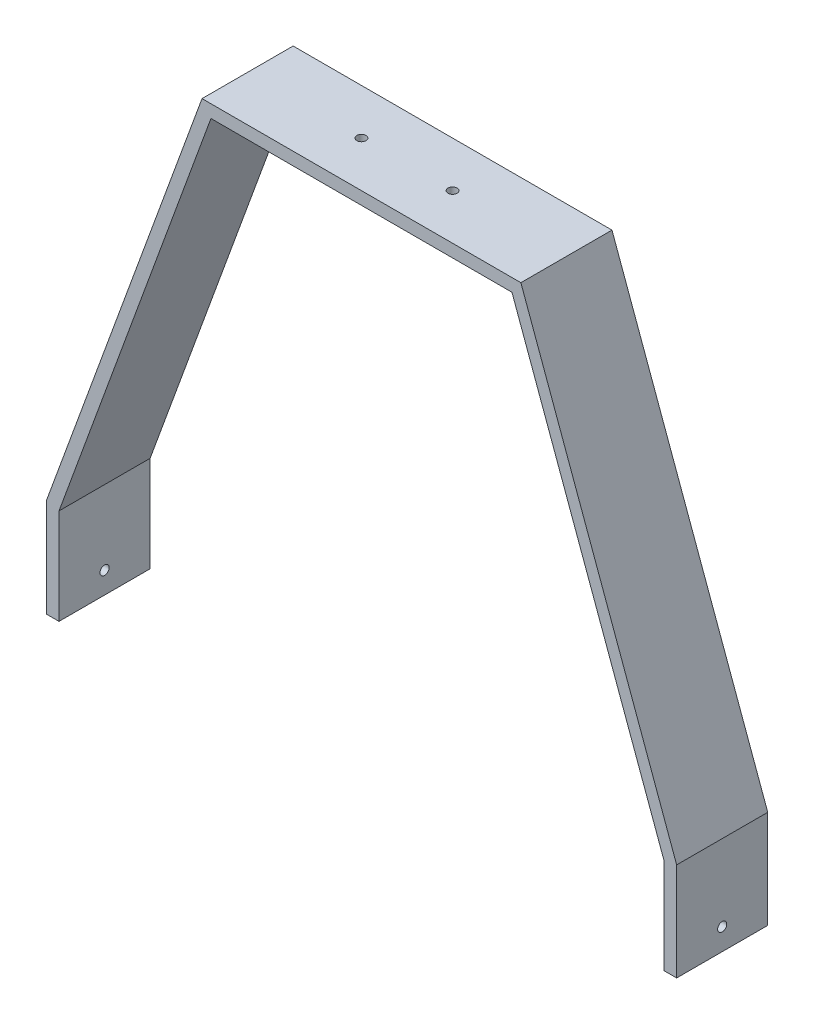
SolidWorks part; units mm, degrees
ref_plane "Front Plane" through (0, 0, 0) normal (0, 0, 1) x (1, 0, 0)
ref_plane "Top Plane" through (0, 0, 0) normal (0, 1, 0) x (1, 0, 0)
ref_plane "Right Plane" through (0, 0, 0) normal (1, 0, 0) x (0, 0, -1)
sketch "Sketch1" plane through (0, 0, 0) normal (0, 0, 1) x (1, 0, 0)
  line L0 (0, 0) -> (175, 0) construction
  line L1 (0, 0) -> (-85.5, -234)
  line L2 (87.5, 0) -> (87.5, 70.6967) construction
  line L4 (4.8949, -7) -> (-78.5, -235.2388)
  line L5 (175, -59.8989) -> (0, -59.8989) construction
  line L6 (175, -59.8989) -> (175, 90.1011) construction
  line L7 (175, 90.1011) -> (0, 90.1011) construction
  line L8 (0, -59.8989) -> (0, 90.1011) construction
  line L11 (170.1051, -7) -> (253.5, -235.2388)
  line L12 (175, 0) -> (260.5, -234)
  line L15 (0, 0) -> (175, 0)
  line L16 (170.1051, -7) -> (4.8949, -7)
  line L17 (87.5, 0) -> (87.5, -45.9968) construction
  line L19 (260.5, -234) -> (260.5, -287.7575)
  line L20 (260.5, -287.7575) -> (253.5, -287.7575)
  line L21 (253.5, -235.2388) -> (253.5, -287.7575)
  line L22 (-85.5, -287.7575) -> (-78.5, -287.7575)
  line L23 (-78.5, -235.2388) -> (-78.5, -287.7575)
  line L25 (-85.5, -234) -> (-85.5, -287.7575)
  point P17 (251.6016, -230.0431)
  dimension "D1" = 175
  dimension "D2" = 234
  dimension "D3" = 85.5
  dimension "D4" = 150
  dimension "D5" = 7
  dimension "D6" = 7
  dimension "D7" = 7
extrude "Boss-Extrude2" add sketch "Sketch1" along normal blind 50
sketch "Sketch2" plane through (260.5, 0, 0) normal (1, 0, 0) x (0, 0, -1)
  line L0 (-50, -275.8912) -> (-25, -275.8912) construction
  line L2 (-25, -275.8912) -> (-25, -287.7575) construction
  line L3 (-50, -287.7575) -> (0, -287.7575) construction
  circle A0 centre (-25, -275.8912) radius 2.5
  point P0 (-24.6271, -287.7575)
  point P2 (-23.3175, -260.8788)
  dimension "D1" = 5
extrude "Cut-Extrude1" cut sketch "Sketch2" against normal through all
sketch "Sketch3" plane through (0, 0, 0) normal (0, 1, 0) x (1, 0, 0)
  line L0 (175, -25) -> (0, -25) construction
  line L1 (175, -50) -> (175, 0) construction
  line L2 (0, -50) -> (0, 0) construction
  line L3 (87.5, 0) -> (87.5, -50) construction
  line L4 (175, 0) -> (0, 0) construction
  line L5 (175, -50) -> (0, -50) construction
  circle A0 centre (112.5, -25) radius 2.5
  circle A1 centre (62.5, -25) radius 2.5
  dimension "D1" = 5
  dimension "D2" = 25
extrude "Cut-Extrude2" cut sketch "Sketch3" against normal through all
